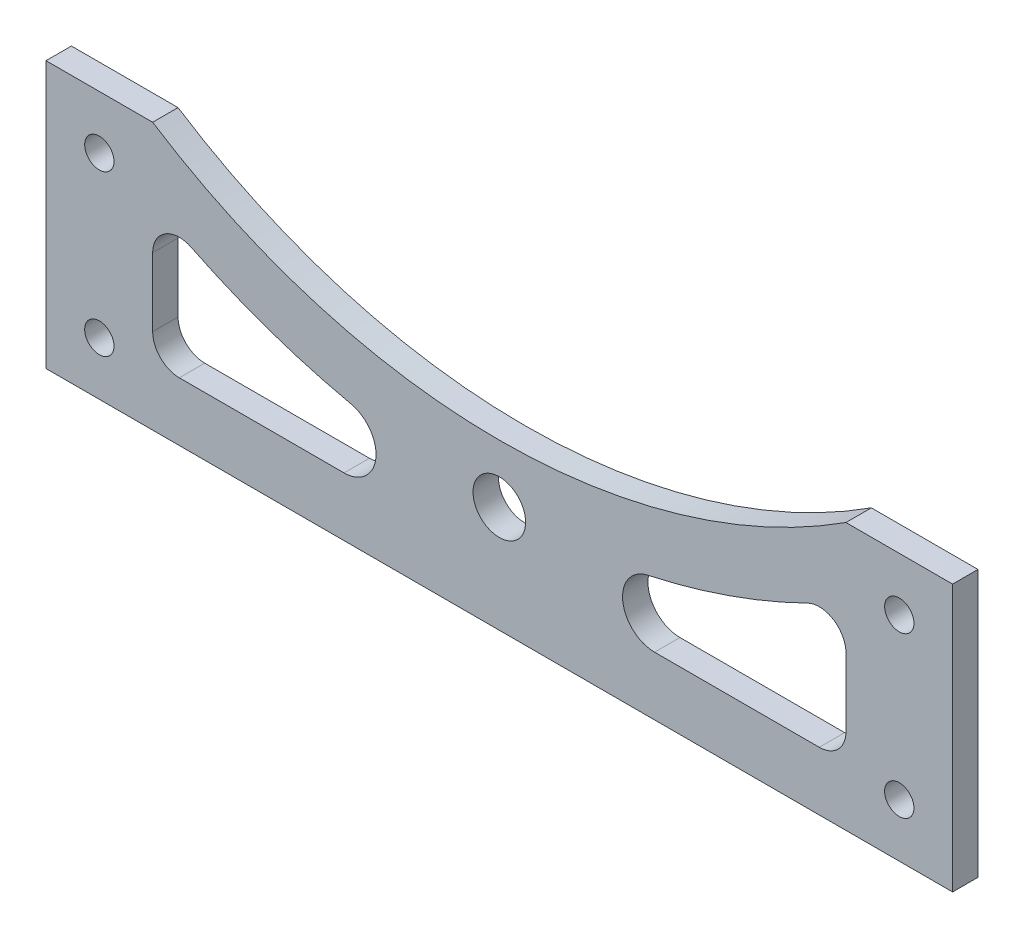
SolidWorks part; units mm, degrees
ref_plane "Front Plane" through (0, 0, 0) normal (0, 0, 1) x (1, 0, 0)
ref_plane "Top Plane" through (0, 0, 0) normal (0, 1, 0) x (1, 0, 0)
ref_plane "Right Plane" through (0, 0, 0) normal (1, 0, 0) x (0, 0, -1)
sketch "Sketch1" plane through (0, 0, 0) normal (0, 0, 1) x (1, 0, 0)
  line L0 (-85, 0) -> (85, 0)
  line L1 (85, 0) -> (85, 50)
  line L2 (85, 50) -> (65, 50)
  line L3 (-85, 0) -> (-85, 50)
  line L4 (-85, 50) -> (-65, 50)
  line L5 (-75, 50) -> (-75, 40) construction
  line L6 (75, 50) -> (75, 40) construction
  line L7 (-65, 28.822) -> (-65, 16)
  line L8 (-60, 11) -> (-29.1119, 11)
  line L9 (65, 28.822) -> (65, 16)
  line L10 (60, 11) -> (29.1119, 11)
  circle A0 centre (0, 20) radius 4.93
  arc A1 (-65, 50) -> (65, 50) centre (0, 150.8712) ccw
  circle A2 centre (-75, 40) radius 2.75
  circle A3 centre (-75, 10) radius 2.75
  circle A4 centre (75, 40) radius 2.75
  circle A5 centre (75, 10) radius 2.75
  arc A6 (-57.7941, 33.3091) -> (-27.8369, 22.863) centre (0, 150.8712) ccw
  arc A7 (-29.1119, 11) -> (-27.8369, 22.863) centre (-29.1119, 17) ccw
  arc A8 (27.8369, 22.863) -> (29.1119, 11) centre (29.1119, 17) ccw
  arc A9 (-70.9583, 40.7535) -> (70.9583, 40.7535) centre (0, 150.8712) ccw construction
  arc A10 (65, 28.822) -> (57.7941, 33.3091) centre (60, 28.822) ccw
  arc A11 (65, 16) -> (60, 11) centre (60, 16) cw
  arc A12 (-65, 16) -> (-60, 11) centre (-60, 16) ccw
  arc A13 (-57.7941, 33.3091) -> (-65, 28.822) centre (-60, 28.822) ccw
  arc A14 (27.8369, 22.863) -> (57.7941, 33.3091) centre (0, 150.8712) ccw
  dimension "D5" = 9.86
  dimension "D6" = 120
  dimension "D7" = 5.5
  dimension "D13" = 5
  dimension "D15" = 6
  dimension "D1" = 50
  dimension "D2" = 20
  dimension "D3" = 20
  dimension "D4" = 170
  dimension "D8" = 10
  dimension "D9" = 10
  dimension "D11" = 11
  dimension "D10" = 11
extrude "Boss-Extrude1" add sketch "Sketch1" along normal blind 4.7625
